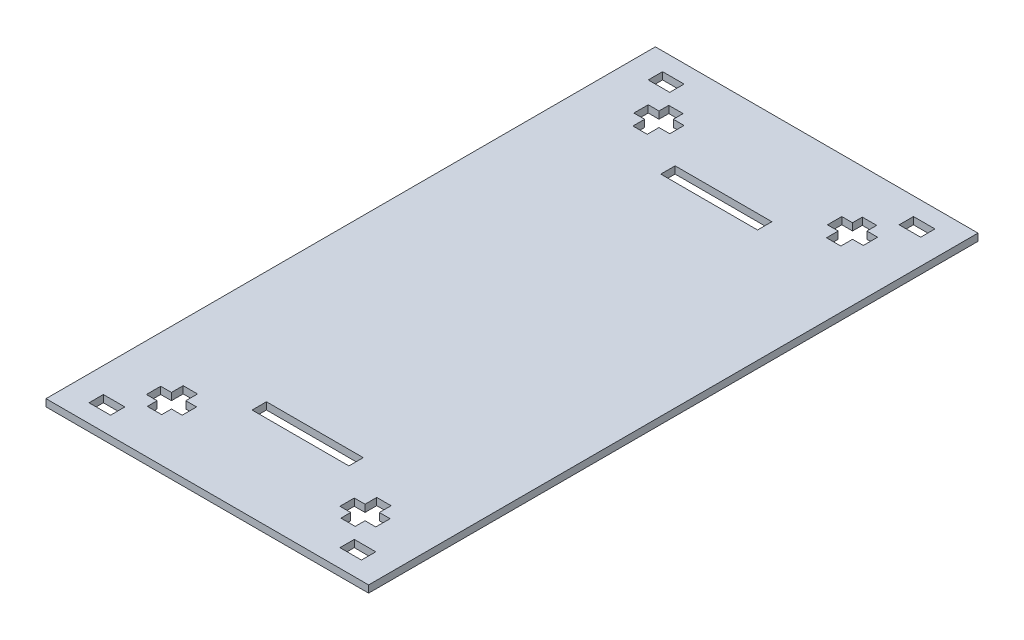
SolidWorks part; units mm, degrees
material "Hexcel AS4C (3000 丝)"
ref_plane "Front" through (0, 0, 0) normal (0, 0, 1) x (1, 0, 0)
ref_plane "Top" through (0, 0, 0) normal (0, 1, 0) x (1, 0, 0)
ref_plane "Right" through (0, 0, 0) normal (1, 0, 0) x (0, 0, -1)
sketch "草图1" plane through (0, 0, 0) normal (0, 1, 0) x (1, 0, 0)
  line L0 (0, 0) -> (0, -78) construction
  line L1 (0, -78) -> (35, -78) construction
  line L2 (0, 0) -> (35, 0) construction
  line L3 (0, 0) -> (0, 85) construction
  line L4 (0, 85) -> (45, 85) construction
  line L5 (45, 85) -> (45, -85) construction
  line L6 (0, 0) -> (-27, 0) construction
  line L7 (-27, 0) -> (-27, -68) construction
  line L8 (-29, -66) -> (-29, -62.7311)
  line L9 (-29, -62.7311) -> (-25, -62.7311)
  line L10 (-25, -62.7311) -> (-25, -66)
  line L11 (-25, -72.7311) -> (-29, -72.7311)
  line L12 (-29, -72.7311) -> (-29, -70)
  line L13 (-25, -66) -> (-22, -66)
  line L14 (-22, -66) -> (-22, -70)
  line L15 (-22, -70) -> (-25, -70)
  line L16 (-32, -70) -> (-32, -66)
  line L17 (-32, -66) -> (-29, -66)
  line L18 (-29, -70) -> (-32, -70)
  line L19 (-25, -70) -> (-25, -72.7311)
  line L20 (29, -72.7311) -> (29, -70)
  line L21 (25, -72.7311) -> (29, -72.7311)
  line L22 (25, -70) -> (25, -72.7311)
  line L23 (22, -70) -> (25, -70)
  line L24 (22, -66) -> (22, -70)
  line L25 (25, -66) -> (22, -66)
  line L26 (25, -62.7311) -> (25, -66)
  line L27 (29, -62.7311) -> (25, -62.7311)
  line L28 (29, -66) -> (29, -62.7311)
  line L29 (32, -66) -> (29, -66)
  line L30 (32, -70) -> (32, -66)
  line L31 (29, -70) -> (32, -70)
  line L32 (25, 72.7311) -> (29, 72.7311)
  line L33 (25, 70) -> (25, 72.7311)
  line L34 (22, 70) -> (25, 70)
  line L35 (22, 66) -> (22, 70)
  line L36 (25, 66) -> (22, 66)
  line L37 (25, 62.7311) -> (25, 66)
  line L38 (29, 62.7311) -> (25, 62.7311)
  line L39 (29, 66) -> (29, 62.7311)
  line L40 (32, 66) -> (29, 66)
  line L41 (32, 70) -> (32, 66)
  line L42 (29, 70) -> (32, 70)
  line L43 (29, 72.7311) -> (29, 70)
  line L44 (-29, 72.7311) -> (-29, 70)
  line L45 (-25, 72.7311) -> (-29, 72.7311)
  line L46 (-25, 70) -> (-25, 72.7311)
  line L47 (-22, 70) -> (-25, 70)
  line L48 (-22, 66) -> (-22, 70)
  line L49 (-25, 66) -> (-22, 66)
  line L50 (-25, 62.7311) -> (-25, 66)
  line L51 (-29, 62.7311) -> (-25, 62.7311)
  line L52 (-29, 66) -> (-29, 62.7311)
  line L53 (-32, 66) -> (-29, 66)
  line L54 (-32, 70) -> (-32, 66)
  line L55 (-29, 70) -> (-32, 70)
  line L56 (-45, 85) -> (45, 85)
  line L57 (45, 85) -> (45, -85)
  line L58 (-45, -85) -> (45, -85)
  line L59 (-45, 85) -> (-45, -85)
  line L60 (35, -80) -> (38, -80)
  line L61 (38, -80) -> (38, -76)
  line L62 (38, -76) -> (32, -76)
  line L63 (32, -76) -> (32, -80)
  line L64 (32, -80) -> (35, -80)
  line L65 (-32, -76) -> (-32, -80)
  line L66 (-38, -76) -> (-32, -76)
  line L67 (-38, -80) -> (-38, -76)
  line L68 (-35, -80) -> (-38, -80)
  line L69 (-32, -80) -> (-35, -80)
  line L70 (32, 76) -> (32, 80)
  line L71 (38, 76) -> (32, 76)
  line L72 (38, 80) -> (38, 76)
  line L73 (35, 80) -> (38, 80)
  line L74 (32, 80) -> (35, 80)
  line L75 (-38, 76) -> (-32, 76)
  line L76 (-38, 80) -> (-38, 76)
  line L77 (-35, 80) -> (-38, 80)
  line L78 (-32, 80) -> (-35, 80)
  line L79 (-32, 76) -> (-32, 80)
  line L80 (-13.5, 0) -> (-13.5, 55) construction
  line L81 (-13.5, 55) -> (13.5, 55) construction
  line L82 (13.5, 55) -> (13.5, 59) construction
  line L83 (-13.5, 55) -> (13.5, 55)
  line L84 (13.5, 55) -> (13.5, 59)
  line L85 (13.5, 59) -> (-13.5, 59)
  line L86 (-13.5, 59) -> (-13.5, 55)
  line L87 (13.5, -59) -> (-13.5, -59)
  line L88 (13.5, -55) -> (13.5, -59)
  line L89 (-13.5, -55) -> (13.5, -55)
  line L90 (-13.5, -59) -> (-13.5, -55)
  point P65 (45, 0)
  point P68 (0, -85)
extrude "凸台-拉伸1" add sketch "草图1" along normal blind 2
